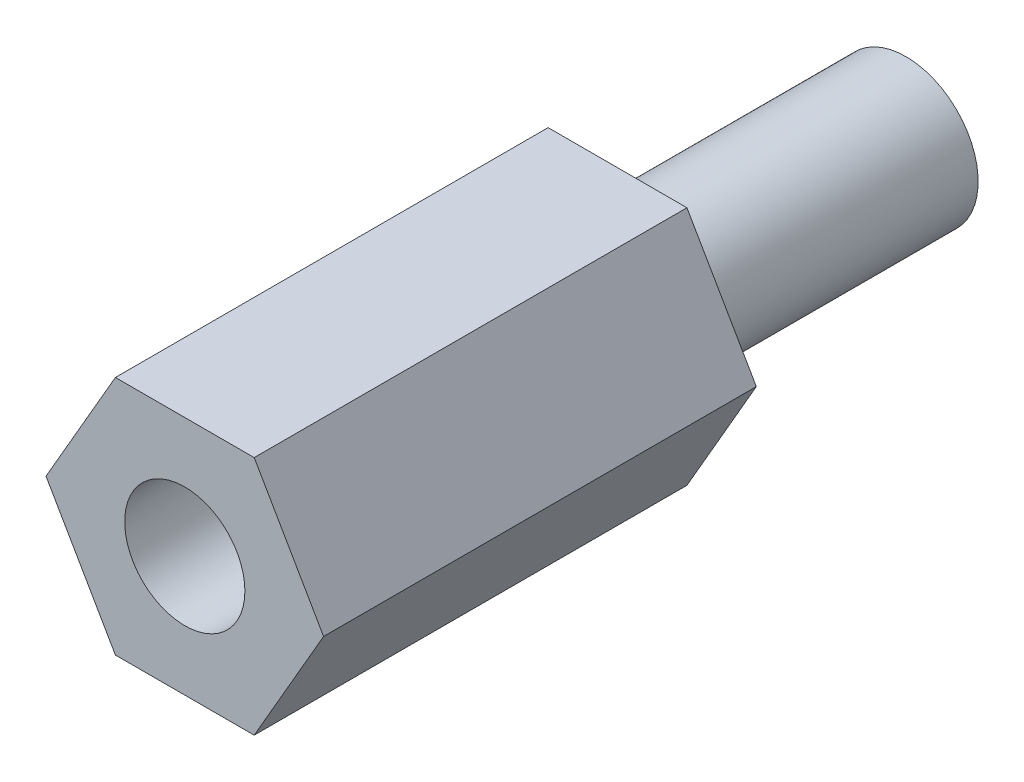
SolidWorks part; units mm, degrees
material "黃銅"
ref_plane "前基準面" through (0, 0, 0) normal (0, 0, 1) x (1, 0, 0)
ref_plane "上基準面" through (0, 0, 0) normal (0, 1, 0) x (1, 0, 0)
ref_plane "右基準面" through (0, 0, 0) normal (1, 0, 0) x (0, 0, -1)
sketch "草圖1" plane through (0, 0, 0) normal (0, 0, 1) x (1, 0, 0)
  line L1 (-1.4434, 2.5) -> (-2.8868, 0)
  line L2 (-2.8868, 0) -> (-1.4434, -2.5)
  line L3 (-1.4434, -2.5) -> (1.4434, -2.5)
  line L4 (1.4434, -2.5) -> (2.8868, 0)
  line L5 (2.8868, 0) -> (1.4434, 2.5)
  line L6 (1.4434, 2.5) -> (-1.4434, 2.5)
  circle A0 centre (0, 0) radius 2.5 construction
  dimension "D1" = 5
extrude "填料-伸長1" add sketch "草圖1" along normal blind 9
sketch "草圖4" plane through (0, 0, 0) normal (0, 0, -1) x (-1, 0, 0)
  circle A0 centre (0, 0) radius 1.5
  dimension "D1" = 3
extrude "填料-伸長2" add sketch "草圖4" along normal blind 6
hole_wizard "M3x0.5 螺紋孔1" positions "草圖2" profile "草圖3" tap size "M3x0.5" standard "Ansi Metric"
sketch "草圖2" plane through (0, 0, 9) normal (0, 0, 1) x (1, 0, 0)
  point P0 (0, 0)
sketch "草圖3" plane through (0, 0, 9) normal (1, 0, 0) x (0, -1, 0)
  line L0 (0, 0) -> (0, 8.2511)
  line L1 (0, 8.2511) -> (1.25, 7.5)
  line L2 (1.25, 7.5) -> (1.25, 0)
  line L5 (1.25, 0) -> (0, 0)
  line L10 (0, 8.2511) -> (-1.25, 7.5) construction
  line L11 (0, -6.35) -> (0, 107.95) construction
  dimension "螺孔鑽直徑" = 2.5
  dimension "螺孔鑽深度" = 7.5
  dimension "導頭角度" = 118
